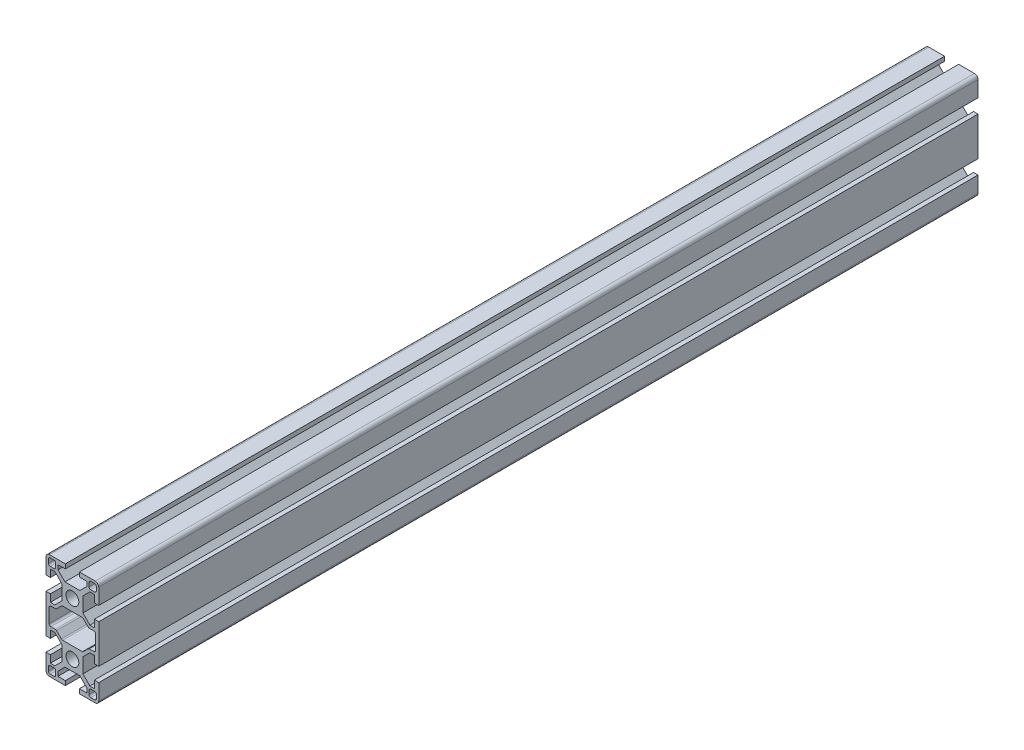
SolidWorks part; units mm, degrees
ref_plane "Front Plane" through (0, 0, 0) normal (0, 0, 1) x (1, 0, 0)
ref_plane "Top Plane" through (0, 0, 0) normal (0, 1, 0) x (1, 0, 0)
ref_plane "Right Plane" through (0, 0, 0) normal (1, 0, 0) x (0, 0, -1)
sketch "Sketch1" plane through (0, 0, 0) normal (0, 0, 1) x (1, 0, 0)
  line B0 (-10.464, -39.464) -> (-12.6216, -39.464)
  arc B1 (-12.6216, -39.464) -> (-13.6216, -40.464) centre (-12.6216, -40.464) ccw
  line B2 (-13.6216, -40.464) -> (-13.6216, -42.6216)
  arc B3 (-13.6216, -42.6216) -> (-12.6216, -43.6216) centre (-12.6216, -42.6216) ccw
  line B4 (-12.6216, -43.6216) -> (-10.464, -43.6216)
  arc B5 (-10.464, -43.6216) -> (-9.464, -42.6216) centre (-10.464, -42.6216) ccw
  line B6 (-9.464, -42.6216) -> (-9.464, -40.464)
  arc B7 (-9.464, -40.464) -> (-10.464, -39.464) centre (-10.464, -40.464) ccw
  line B8 (9.0111, -9.6201) -> (6.2688, -6.8778)
  arc B9 (6.2688, -6.8778) -> (5.5616, -6.5849) centre (5.5616, -7.5849) ccw
  line B10 (5.5616, -6.5849) -> (-5.5616, -6.5849)
  arc B11 (-5.5616, -6.5849) -> (-6.2688, -6.8778) centre (-5.5616, -7.5849) ccw
  line B12 (-6.2688, -6.8778) -> (-9.0111, -9.6201)
  arc B13 (-9.7182, -9.913) -> (-9.0111, -9.6201) centre (-9.7182, -8.913) ccw
  line B14 (-9.7182, -9.913) -> (-12.2496, -9.913)
  arc B15 (-12.2496, -9.913) -> (-13.2496, -10.913) centre (-12.2496, -10.913) ccw
  line B16 (-13.2496, -10.913) -> (-13.2496, -19.087)
  arc B17 (-13.2496, -19.087) -> (-12.2496, -20.087) centre (-12.2496, -19.087) ccw
  line B18 (-12.2496, -20.087) -> (-9.7182, -20.087)
  arc B19 (-9.0111, -20.3799) -> (-9.7182, -20.087) centre (-9.7182, -21.087) ccw
  line B20 (-9.0111, -20.3799) -> (-6.2688, -23.1222)
  arc B21 (-6.2688, -23.1222) -> (-5.5616, -23.4151) centre (-5.5616, -22.4151) ccw
  line B22 (-5.5616, -23.4151) -> (5.5616, -23.4151)
  arc B23 (5.5616, -23.4151) -> (6.2688, -23.1222) centre (5.5616, -22.4151) ccw
  line B24 (6.2688, -23.1222) -> (9.0111, -20.3799)
  arc B25 (9.7182, -20.087) -> (9.0111, -20.3799) centre (9.7182, -21.087) ccw
  line B26 (9.7182, -20.087) -> (12.2496, -20.087)
  arc B27 (12.2496, -20.087) -> (13.2496, -19.087) centre (12.2496, -19.087) ccw
  line B28 (13.2496, -19.087) -> (13.2496, -10.913)
  arc B29 (13.2496, -10.913) -> (12.2496, -9.913) centre (12.2496, -10.913) ccw
  line B30 (12.2496, -9.913) -> (9.7182, -9.913)
  arc B31 (9.0111, -9.6201) -> (9.7182, -9.913) centre (9.7182, -8.913) ccw
  line B32 (9.464, -40.464) -> (9.464, -42.6216)
  arc B33 (9.464, -42.6216) -> (10.464, -43.6216) centre (10.464, -42.6216) ccw
  line B34 (10.464, -43.6216) -> (12.6216, -43.6216)
  arc B35 (12.6216, -43.6216) -> (13.6216, -42.6216) centre (12.6216, -42.6216) ccw
  line B36 (13.6216, -42.6216) -> (13.6216, -40.464)
  arc B37 (13.6216, -40.464) -> (12.6216, -39.464) centre (12.6216, -40.464) ccw
  line B38 (12.6216, -39.464) -> (10.464, -39.464)
  arc B39 (10.464, -39.464) -> (9.464, -40.464) centre (10.464, -40.464) ccw
  circle B40 centre (0, -30) radius 3.65
  line B41 (-15, -34) -> (-15, -43)
  arc B42 (-15, -43) -> (-13, -45) centre (-13, -43) ccw
  line B43 (-13, -45) -> (-4, -45)
  line B44 (-4, -45) -> (-4, -42.5)
  line B45 (-4, -42.5) -> (-8.2022, -42.5)
  line B46 (-8.2022, -42.5) -> (-8.2022, -39.9554)
  line B47 (-8.2022, -39.9554) -> (-4.2226, -35.9759)
  line B48 (-4.2226, -35.9759) -> (4.2226, -35.9759)
  line B49 (4.2226, -35.9759) -> (8.2022, -39.9554)
  line B50 (8.2022, -39.9554) -> (8.2022, -42.5)
  line B51 (8.2022, -42.5) -> (4, -42.5)
  line B52 (4, -42.5) -> (4, -45)
  line B53 (4, -45) -> (13, -45)
  arc B54 (13, -45) -> (15, -43) centre (13, -43) ccw
  line B55 (15, -43) -> (15, -34)
  line B56 (15, -34) -> (12.5, -34)
  line B57 (12.5, -34) -> (12.5, -38.2022)
  line B58 (12.5, -38.2022) -> (9.9554, -38.2022)
  line B59 (9.9554, -38.2022) -> (5.9759, -34.2226)
  line B60 (5.9759, -34.2226) -> (5.9759, -25.7774)
  line B61 (5.9759, -25.7774) -> (9.9554, -21.7978)
  line B62 (9.9554, -21.7978) -> (12.5, -21.7978)
  line B63 (12.5, -21.7978) -> (12.5, -26)
  line B64 (12.5, -26) -> (15, -26)
  line B65 (15, -26) -> (15, -4)
  line B66 (15, -4) -> (12.5, -4)
  line B67 (12.5, -4) -> (12.5, -8.2022)
  line B68 (12.5, -8.2022) -> (9.9554, -8.2022)
  line B69 (9.9554, -8.2022) -> (5.9759, -4.2226)
  line B70 (5.9759, -4.2226) -> (5.9759, 4.2226)
  line B71 (5.9759, 4.2226) -> (9.9554, 8.2022)
  line B72 (9.9554, 8.2022) -> (12.5, 8.2022)
  line B73 (12.5, 8.2022) -> (12.5, 4)
  line B74 (12.5, 4) -> (15, 4)
  line B75 (15, 4) -> (15, 13)
  arc B76 (15, 13) -> (13, 15) centre (13, 13) ccw
  line B77 (13, 15) -> (4, 15)
  line B78 (4, 15) -> (4, 12.5)
  line B79 (4, 12.5) -> (8.2022, 12.5)
  line B80 (8.2022, 12.5) -> (8.2022, 9.9554)
  line B81 (8.2022, 9.9554) -> (4.2226, 5.9759)
  line B82 (4.2226, 5.9759) -> (-4.2226, 5.9759)
  line B83 (-4.2226, 5.9759) -> (-8.2022, 9.9554)
  line B84 (-8.2022, 9.9554) -> (-8.2022, 12.5)
  line B85 (-8.2022, 12.5) -> (-4, 12.5)
  line B86 (-4, 12.5) -> (-4, 15)
  line B87 (-4, 15) -> (-13, 15)
  arc B88 (-13, 15) -> (-15, 13) centre (-13, 13) ccw
  line B89 (-15, 13) -> (-15, 4)
  line B90 (-15, 4) -> (-12.5, 4)
  line B91 (-12.5, 4) -> (-12.5, 8.2022)
  line B92 (-12.5, 8.2022) -> (-9.9554, 8.2022)
  line B93 (-9.9554, 8.2022) -> (-5.9759, 4.2226)
  line B94 (-5.9759, 4.2226) -> (-5.9759, -4.2226)
  line B95 (-5.9759, -4.2226) -> (-9.9554, -8.2022)
  line B96 (-9.9554, -8.2022) -> (-12.5, -8.2022)
  line B97 (-12.5, -8.2022) -> (-12.5, -4)
  line B98 (-12.5, -4) -> (-15, -4)
  line B99 (-15, -4) -> (-15, -26)
  line B100 (-15, -26) -> (-12.5, -26)
  line B101 (-12.5, -26) -> (-12.5, -21.7978)
  line B102 (-12.5, -21.7978) -> (-9.9554, -21.7978)
  line B103 (-9.9554, -21.7978) -> (-5.9759, -25.7774)
  line B104 (-5.9759, -25.7774) -> (-5.9759, -34.2226)
  line B105 (-5.9759, -34.2226) -> (-9.9554, -38.2022)
  line B106 (-9.9554, -38.2022) -> (-12.5, -38.2022)
  line B107 (-12.5, -38.2022) -> (-12.5, -34)
  line B108 (-12.5, -34) -> (-15, -34)
  circle B109 centre (0, 0) radius 3.65
  line B110 (-9.464, 10.464) -> (-9.464, 12.6216)
  arc B111 (-9.464, 12.6216) -> (-10.464, 13.6216) centre (-10.464, 12.6216) ccw
  line B112 (-10.464, 13.6216) -> (-12.6216, 13.6216)
  arc B113 (-12.6216, 13.6216) -> (-13.6216, 12.6216) centre (-12.6216, 12.6216) ccw
  line B114 (-13.6216, 12.6216) -> (-13.6216, 10.464)
  arc B115 (-13.6216, 10.464) -> (-12.6216, 9.464) centre (-12.6216, 10.464) ccw
  line B116 (-12.6216, 9.464) -> (-10.464, 9.464)
  arc B117 (-10.464, 9.464) -> (-9.464, 10.464) centre (-10.464, 10.464) ccw
  line B118 (10.464, 9.464) -> (12.6216, 9.464)
  arc B119 (12.6216, 9.464) -> (13.6216, 10.464) centre (12.6216, 10.464) ccw
  line B120 (13.6216, 10.464) -> (13.6216, 12.6216)
  arc B121 (13.6216, 12.6216) -> (12.6216, 13.6216) centre (12.6216, 12.6216) ccw
  line B122 (12.6216, 13.6216) -> (10.464, 13.6216)
  arc B123 (10.464, 13.6216) -> (9.464, 12.6216) centre (10.464, 12.6216) ccw
  line B124 (9.464, 12.6216) -> (9.464, 10.464)
  arc B125 (9.464, 10.464) -> (10.464, 9.464) centre (10.464, 10.464) ccw
sketch_block_instance "3060-1"
sketch_block "3060"
extrude "Boss-Extrude1" add sketch "Sketch1" along normal blind 500
